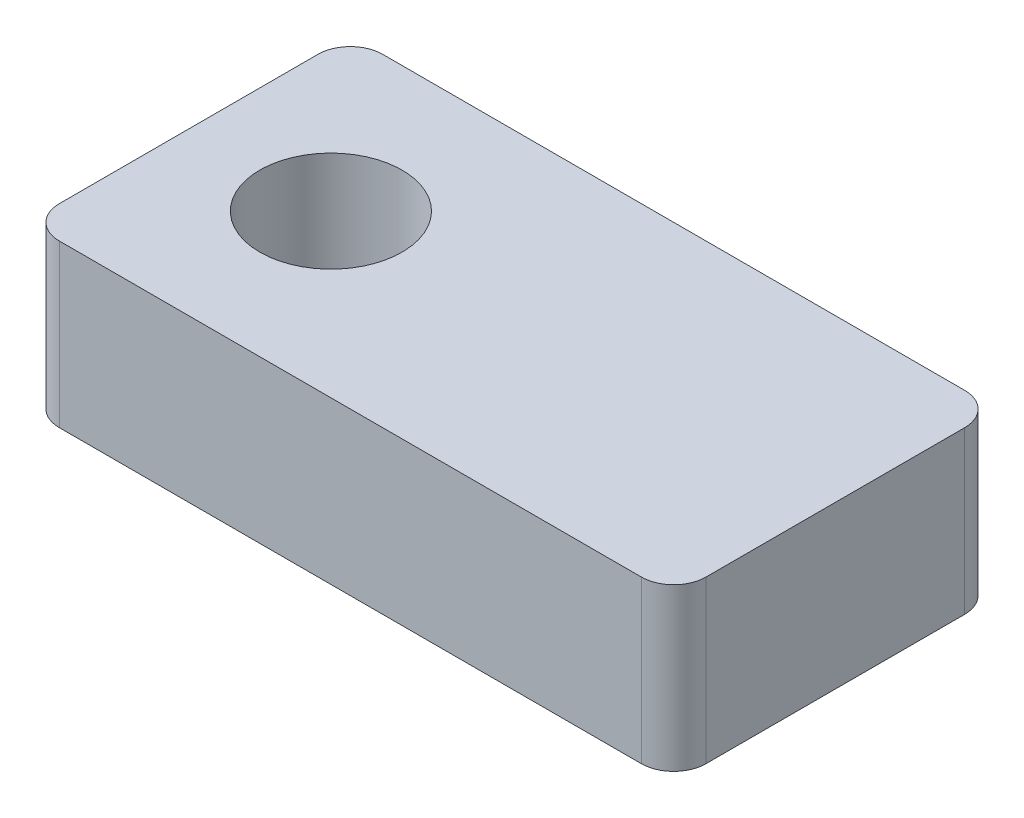
SolidWorks part; units mm, degrees
ref_plane "Front" through (0, 0, 0) normal (0, 0, 1) x (1, 0, 0)
ref_plane "Top" through (0, 0, 0) normal (0, 1, 0) x (1, 0, 0)
ref_plane "Right" through (0, 0, 0) normal (1, 0, 0) x (0, 0, -1)
sketch "Sketch1" plane through (0, 0, 0) normal (0, 1, 0) x (1, 0, 0)
  line L0 (-2.8, 0) -> (0, 0) construction
  line L1 (-5, -2.5) -> (5, -2.5)
  line L2 (-5, -2.5) -> (-5, 2.5)
  line L3 (-5, 2.5) -> (5, 2.5)
  line L4 (5, -2.5) -> (5, 2.5)
  line L5 (-5, -2.5) -> (5, 2.5) construction
  line L6 (-5, 2.5) -> (5, -2.5) construction
  circle A0 centre (-2.8, 0) radius 1.1
  point P0 (0, 0)
  dimension "D1" = 2.2
  dimension "D2" = 10
  dimension "D3" = 2.2
  dimension "D4" = 5
extrude "Boss-Extrude1" add sketch "Sketch1" along normal blind 2.5
fillet "Fillet1" radius 0.5 4 edges at (5, 1.25, 2.5) (5, 1.25, -2.5) (-5, 1.25, -2.5) (-5, 1.25, 2.5)
